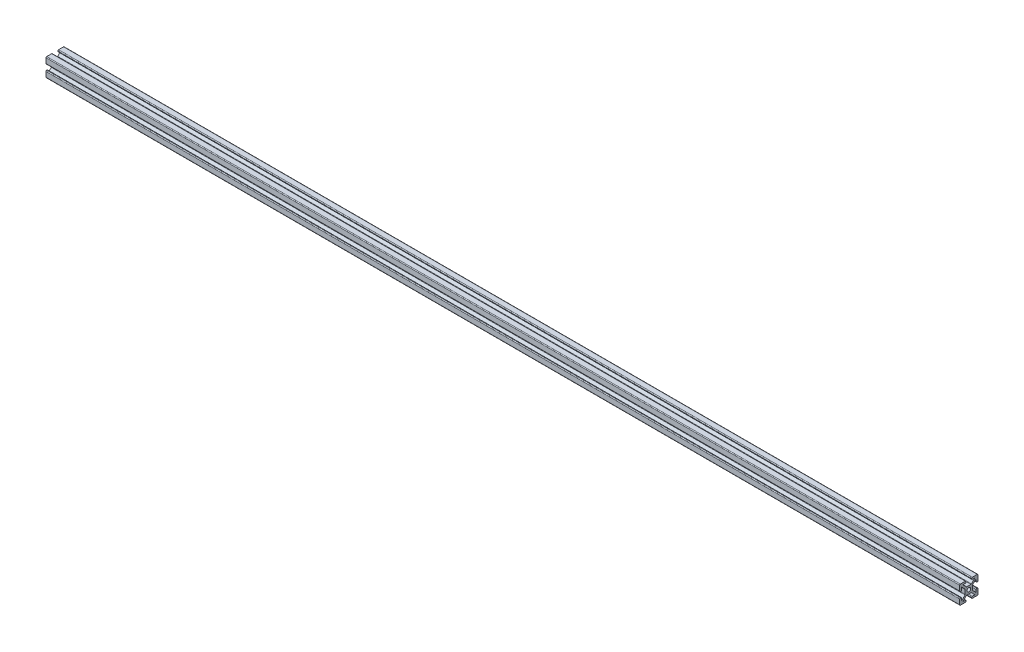
SolidWorks part; units mm, degrees
material "1060 Alloy"
ref_plane "Front Plane" through (0, 0, 0) normal (0, 0, 1) x (1, 0, 0)
ref_plane "Top Plane" through (0, 0, 0) normal (0, 1, 0) x (1, 0, 0)
ref_plane "Right Plane" through (0, 0, 0) normal (1, 0, 0) x (0, 0, -1)
sketch "Sketch2" plane through (0, 0, 0) normal (0, 0, 1) x (1, 0, 0)
  line L0 (-407.6006, 0) -> (592.3994, 0)
  dimension "D1" = 1000
other "Profile 4X4(1)"
ref_plane "Plane1" through (-407.6006, 0, 0) normal (1, 0, 0) x (0, 1, 0)
sketch "Sketch1" plane through (-407.6006, 0, 0) normal (1, 0, 0) x (0, 1, 0)
  line L0 (-3, 9.2) -> (-3, 8.8)
  line L1 (-2.2544, 4) -> (2.2544, 4)
  line L2 (-4, 2.2544) -> (-4, -2.2544)
  line L3 (-2.2544, -4) -> (2.2544, -4)
  line L4 (4, 2.2544) -> (4, -2.2544)
  line L7 (-6.5858, 8) -> (-3.8, 8)
  line L8 (-8, 6.5858) -> (-8, 3.8)
  line L9 (-6.5858, -8) -> (-3.8, -8)
  line L10 (8, 6.5858) -> (8, 3.8)
  line L12 (9.7657, -9.7657) -> (10, -10) construction
  line L13 (-9.2, 10) -> (-3.8, 10)
  line L14 (-10, 9.2) -> (-10, 3.8)
  line L15 (-9.2, -10) -> (-3.8, -10)
  line L16 (10, 9.2) -> (10, 3.8)
  line L17 (-10, 10) -> (-9.7657, 9.7657) construction
  line L18 (-10, -10) -> (-9.7657, -9.7657) construction
  line L21 (3, 9.2) -> (3, 8.8)
  line L22 (3, -9.2) -> (3, -8.8)
  line L23 (-3, -9.2) -> (-3, -8.8)
  line L24 (3.8, 10) -> (9.2, 10)
  line L25 (3.8, 8) -> (6.5858, 8)
  line L26 (-9.2, 3) -> (-8.8, 3)
  line L27 (9.2, 3) -> (8.8, 3)
  line L28 (9.2, -3) -> (8.8, -3)
  line L29 (-9.2, -3) -> (-8.8, -3)
  line L30 (-10, -3.8) -> (-10, -9.2)
  line L31 (-8, -3.8) -> (-8, -6.5858)
  line L32 (8, -3.8) -> (8, -6.5858)
  line L33 (10, -3.8) -> (10, -9.2)
  line L34 (3.8, -8) -> (6.5858, -8)
  line L35 (3.8, -10) -> (9.2, -10)
  line L36 (6.5858, 8) -> (2.8201, 4.2343)
  line L37 (8, 6.5858) -> (4.2343, 2.8201)
  line L38 (8, -6.5858) -> (4.2343, -2.8201)
  line L39 (6.5858, -8) -> (2.8201, -4.2343)
  line L40 (-6.5858, -8) -> (-2.8201, -4.2343)
  line L41 (-8, -6.5858) -> (-4.2343, -2.8201)
  line L42 (-8, 6.5858) -> (-4.2343, 2.8201)
  line L43 (-6.5858, 8) -> (-2.8201, 4.2343)
  line L47 (9.7657, 9.7657) -> (10, 10) construction
  circle A0 centre (0, 0) radius 2
  arc A1 (9.2, -3) -> (10, -3.8) centre (9.2, -3.8) cw
  arc A2 (8.8, -3) -> (8, -3.8) centre (8.8, -3.8) ccw
  arc A3 (3, -9.2) -> (3.8, -10) centre (3.8, -9.2) ccw
  arc A4 (3, -8.8) -> (3.8, -8) centre (3.8, -8.8) cw
  arc A5 (-3, -9.2) -> (-3.8, -10) centre (-3.8, -9.2) cw
  arc A6 (-3, -8.8) -> (-3.8, -8) centre (-3.8, -8.8) ccw
  arc A7 (-8.8, -3) -> (-8, -3.8) centre (-8.8, -3.8) cw
  arc A8 (-9.2, -3) -> (-10, -3.8) centre (-9.2, -3.8) ccw
  arc A9 (-10, -9.2) -> (-9.2, -10) centre (-9.2, -9.2) ccw
  arc A10 (9.2, -10) -> (10, -9.2) centre (9.2, -9.2) ccw
  arc A11 (9.2, 10) -> (10, 9.2) centre (9.2, 9.2) cw
  arc A12 (-9.2, 10) -> (-10, 9.2) centre (-9.2, 9.2) ccw
  arc A13 (9.2, 3) -> (10, 3.8) centre (9.2, 3.8) ccw
  arc A14 (8.8, 3) -> (8, 3.8) centre (8.8, 3.8) cw
  arc A15 (3, 9.2) -> (3.8, 10) centre (3.8, 9.2) cw
  arc A16 (3, 8.8) -> (3.8, 8) centre (3.8, 8.8) ccw
  arc A17 (-3, 9.2) -> (-3.8, 10) centre (-3.8, 9.2) ccw
  arc A18 (-3, 8.8) -> (-3.8, 8) centre (-3.8, 8.8) cw
  arc A19 (-8.8, 3) -> (-8, 3.8) centre (-8.8, 3.8) ccw
  arc A20 (-9.2, 3) -> (-10, 3.8) centre (-9.2, 3.8) cw
  arc A21 (-2.8201, 4.2343) -> (-2.2544, 4) centre (-2.2544, 4.8) ccw
  arc A22 (4.2343, 2.8201) -> (4, 2.2544) centre (4.8, 2.2544) ccw
  arc A23 (2.8201, 4.2343) -> (2.2544, 4) centre (2.2544, 4.8) cw
  arc A24 (4.2343, -2.8201) -> (4, -2.2544) centre (4.8, -2.2544) cw
  arc A25 (2.8201, -4.2343) -> (2.2544, -4) centre (2.2544, -4.8) ccw
  arc A26 (-2.8201, -4.2343) -> (-2.2544, -4) centre (-2.2544, -4.8) cw
  arc A27 (-4.2343, -2.8201) -> (-4, -2.2544) centre (-4.8, -2.2544) ccw
  arc A28 (-4.2343, 2.8201) -> (-4, 2.2544) centre (-4.8, 2.2544) cw
  point P7 (0, 0)
  point P10 (-2.5858, 4)
  point P53 (10, -3)
  point P56 (8, -3)
  point P59 (3, -10)
  point P62 (3, -8)
  point P65 (-3, -10)
  point P68 (-3, -8)
  point P71 (-8, -3)
  point P74 (-10, -3)
  point P89 (10, 3)
  point P92 (8, 3)
  point P95 (3, 10)
  point P98 (3, 8)
  point P101 (-3, 10)
  point P104 (-3, 8)
  point P107 (-8, 3)
  point P110 (-10, 3)
  point P116 (4, 2.5858)
  point P119 (2.5858, 4)
  point P122 (4, -2.5858)
  point P125 (2.5858, -4)
  point P128 (-2.5858, -4)
  point P131 (-4, -2.5858)
  point P134 (-4, 2.5858)
  dimension "D3" = 4
  dimension "D11" = 0.8
  dimension "D12" = 0.8
  dimension "D2" = 0.8
  dimension "D4" = 20
  dimension "D6" = 20
  dimension "D8" = 7
  dimension "D9" = 7
sketch "Sketch3" plane through (0, 4, 0) normal (0, 1, 0) x (1, 0, 0)
  line L0 (592.3994, 0) -> (514.3444, 0) construction
  line L1 (592.3994, 2.2544) -> (592.3994, -2.2544) construction
  circle A0 centre (472.3994, 0) radius 2.5
  dimension "D1" = 5
  dimension "D2" = 120
extrude "Cut-Extrude1" cut sketch "Sketch3" against normal blind 10
